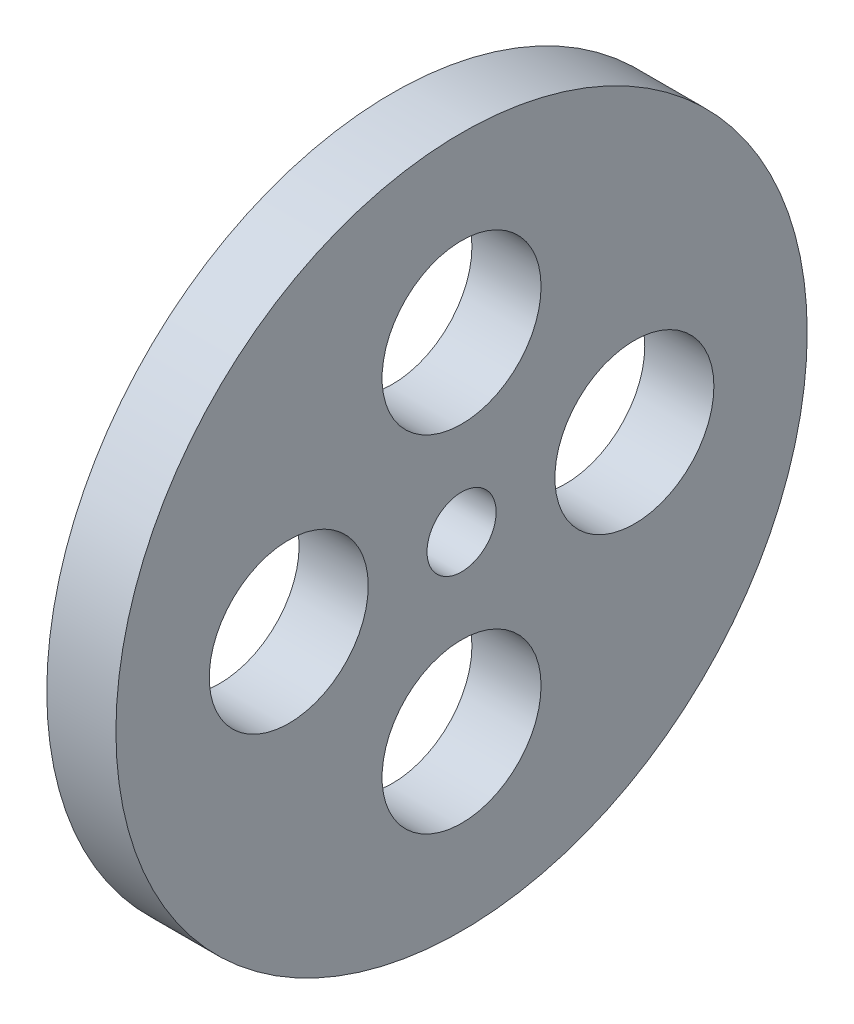
SolidWorks part; units mm, degrees
ref_plane "Front Plane" through (0, 0, 0) normal (0, 0, 1) x (1, 0, 0)
ref_plane "Top Plane" through (0, 0, 0) normal (0, 1, 0) x (1, 0, 0)
ref_plane "Right Plane" through (0, 0, 0) normal (1, 0, 0) x (0, 0, -1)
sketch "Sketch1" plane through (0, 0, 0) normal (1, 0, 0) x (0, 0, -1)
  circle A0 centre (0, 0) radius 50
  circle A1 centre (0, 0) radius 5
  circle A3 centre (-25, 0) radius 11.5
  circle A4 centre (0, 25) radius 11.5
  circle A5 centre (25, 0) radius 11.5
  circle A6 centre (0, -25) radius 11.5
  point P15 (0, 0)
  dimension "D1" = 100
  dimension "D2" = 10
  dimension "D4" = 23
  dimension "D3" = 25
  dimension "D5" = 4
extrude "Boss-Extrude1" add sketch "Sketch1" along normal blind 10
